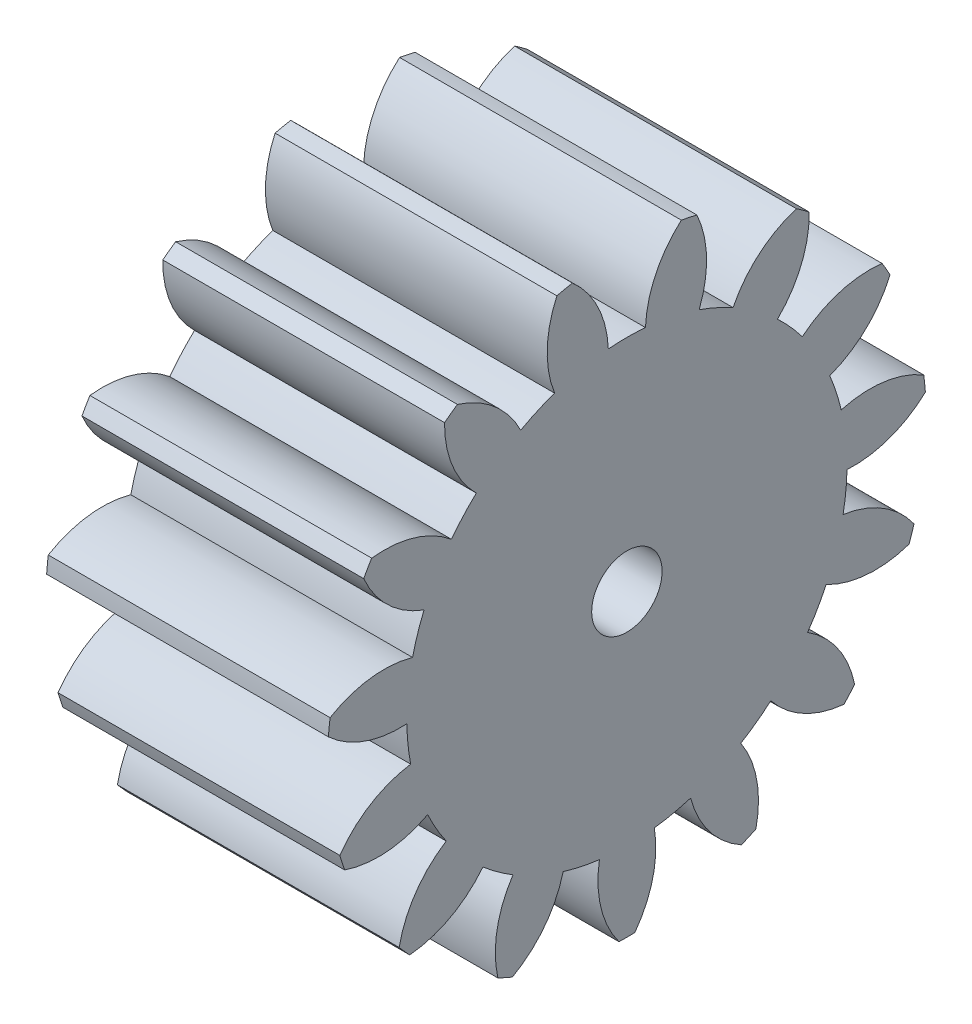
SolidWorks part; units mm, degrees
ref_plane "Plane1" through (0, 0, 0) normal (0, 0, 1) x (1, 0, 0)
ref_plane "Plane2" through (0, 0, 0) normal (0, 1, 0) x (1, 0, 0)
ref_plane "Plane3" through (0, 0, 0) normal (1, 0, 0) x (0, 0, -1)
sketch "HoldingSke" plane through (0, 0, 0) normal (0, 1, 0) x (1, 0, 0)
  line L0 (0, 0) -> (0.3864, -0.1035)
  line L1 (-15, 0) -> (100, 0) construction
  line L2 (0, 0) -> (-2.1039, 2.3779)
  line L3 (0, 0) -> (-11.863, 4.5341)
  line L4 (0, 0) -> (8.3417, 2.2352)
  line L5 (0, 0) -> (-46.8476, -17.4728)
  line L6 (0, 0) -> (-16.5793, -11.1861)
  line L7 (-2.1039, 2.3779) -> (8.6586, 51.2059)
  line L8 (-76.2, 54.61) -> (-75.3, 54.61)
  line L9 (-71.009, 38.7566) -> (-53.1078, 45.2721)
  line L10 (-76.2, 71.12) -> (104.1128, 71.12)
  line L11 (0, 0) -> (-20, 0)
  line L12 (-76.2, 101.6) -> (-76.113, 101.6)
  line L13 (24.9733, 27.94) -> (52.9518, 28.4284)
  line L14 (24.9733, 27.94) -> (24.9743, 27.94)
  line L15 (24.9733, 27.94) -> (100.4006, 29.5858)
  line L16 (-63.627, -2.5) -> (-12.827, -2.5)
  circle A0 centre (0, 0) radius 2.5
  circle A1 centre (0, 0) radius 15.624
  circle A2 centre (0, 0) radius 37.5
  circle A3 centre (0, 0) radius 2.5
  dimension "MHD" = 31.248
  dimension "Hub_dia" = 75
  dimension "Bore" = 5
  dimension "MBD" = 5
  dimension "Num_teeth" = 15
  dimension "Pitch" = 0.4
  dimension "Overall_len" = 50
  dimension "Show_teeth" = 15
  dimension "Thickness" = 20
  dimension "OAL" = 50.0001
  dimension "T_dim" = 0.9
  dimension "Ap" = 20
  dimension "H" = 19.05
  dimension "Pitch_radius" = 180.3128
  dimension "Width" = 20
  dimension "Backlash" = 0.087
  dimension "Addendum_fac" = 1
  dimension "Dedendum_fac" = 1.25
  dimension "Clearance_fac" = 0.25
  dimension "Dedendum_add" = 0.001
  dimension "Module" = 2.5
sketch "BasProSke" plane through (0, 0, 0) normal (0, 1, 0) x (1, 0, 0)
  line L0 (-10, 0) -> (60, 0) construction
  line L1 (0, 0) -> (0, 21.25)
  line L2 (0, 0) -> (20, 0)
  line L3 (20, 0) -> (20, 21.25)
  line L4 (20, 21.25) -> (0, 21.25)
  dimension "Thickness" = 20
  dimension "Diameter" = 42.5
revolve "Base-Revolve" add sketch "BasProSke" angle 360 about L0
sketch "TooCutSke" plane through (0, 0, 0) normal (1, 0, 0) x (0, 0, -1)
  line L1 (0, 0) -> (0, 107) construction
  line L2 (0, 0) -> (-2.112, 18.6307) construction
  line L3 (0, 0) -> (-7.7604, 36.5097) construction
  line L4 (-2.112, 18.6307) -> (-3.8802, 18.2548) construction
  arc A0 (1.3173, 15.5684) -> (-1.3173, 15.5684) centre (0, 0) ccw
  arc A1 (3.8889, 20.917) -> (-3.8889, 20.917) centre (0, 0) ccw
  circle A2 centre (0, 0) radius 18.75 construction
  circle A3 centre (0, 0) radius 17.6192 construction
  arc A4 (-1.3173, 15.5684) -> (-3.8889, 20.917) centre (-8.8109, 15.258) ccw
  arc A5 (3.8889, 20.917) -> (1.3173, 15.5684) centre (8.8109, 15.258) ccw
  dimension "Root_dia" = 31.248
  dimension "Overcut_dia" = 42.5508
  dimension "Pitch_dia" = 37.5
  dimension "Base_dia" = 35.2385
  dimension "Flank_rad" = 7.5
  dimension "Half_ang" = 12
  dimension "Half_CT" = 1.8077
extrude "ToothCut" cut sketch "TooCutSke" along normal through all
fillet "Breaks" [suppressed] radius 0.05
fillet "RootFillets" [suppressed] radius 0.626
pattern_circular "TeethCuts" count 15 every 24 about axis through (-10, 0, 0) along (1, 0, 0) of "ToothCut", "RootFillets", "Breaks"
sketch "HubNeaOneSke" plane through (0, 0, 0) normal (-1, 0, 0) x (0, 0, 1)
  circle A0 centre (0, 0) radius 15.624
  dimension "Diameter" = 31.248
extrude "HubNearOne" [suppressed] add sketch "HubNeaOneSke" along normal blind 30.0001
sketch "HubNeaBotSke" plane through (0, 0, 0) normal (-1, 0, 0) x (0, 0, 1)
  circle A0 centre (0, 0) radius 15.624
  dimension "Diameter" = 31.248
extrude "HubNearBoth" [suppressed] add sketch "HubNeaBotSke" along normal blind 15
ref_plane "FarPln" through (20, 0, 0) normal (1, 0, 0) x (0, 0, -1)
sketch "HubFarSke" plane through (20, 0, 0) normal (1, 0, 0) x (0, 0, -1)
  circle A0 centre (0, 0) radius 15.624
  dimension "Diameter" = 31.248
extrude "HubFar" [suppressed] add sketch "HubFarSke" along normal blind 15
sketch "BorSke" plane through (0, 0, 0) normal (1, 0, 0) x (0, 0, -1)
  circle A0 centre (0, 0) radius 2.5
  dimension "Diameter" = 5
extrude "Bore" cut sketch "BorSke" along normal mid plane 100.0001
sketch "KeySke" plane through (0, 0, 0) normal (1, 0, 0) x (0, 0, -1)
  line L0 (-1, 0) -> (-1, 3.4)
  line L1 (-1, 3.4) -> (1, 3.4)
  line L2 (1, 3.4) -> (1, 0)
  line L3 (0, 0) -> (0, 34) construction
  line L4 (-1, 0) -> (1, 0)
  dimension "Offset" = 3.4
extrude "Keyway" [suppressed] cut sketch "KeySke" along normal mid plane 100.0001
pattern_circular "Keyway2" [suppressed] count 2 every 90 about axis through (-10, 0, 0) along (1, 0, 0)
equation "' \"Module@HoldingSke\" = 6.35"
equation "' \"Num_teeth@HoldingSke\" = 12"
equation "' \"Ap@HoldingSke\" =  20"
equation "' \"Ap@HoldingSke\" = 20"
equation "' \"Width@HoldingSke\" = 0.5 * 25.4"
equation "' \"Hub_dia@HoldingSke\"= 1 * 25.4"
equation "' \"Hub_dia@HoldingSke\" = 1 * 25.4"
equation "' \"Overall_len@HoldingSke\" = 1.0 * 25.4"
equation "' \"Bore@HoldingSke\" = 0.75 * 25.4"
equation "' \"T_dim@HoldingSke\" = 0.1 * 25.4"
equation "' \"Width@KeySke\" = 0.25 * 25.4"
equation "' \"Show_teeth@HoldingSke\" = 13"
equation "' \"Backlash@HoldingSke\" = 0.009 * 25.4"
equation "' \"Addendum_fac@HoldingSke\" = 1.0"
equation "' \"Dedendum_fac@HoldingSke\" = 1.25"
equation "' \"Dedendum_add@HoldingSke\" = 0.00005 * 25.4"
equation "' \"Clearance_fac@HoldingSke\" = 0.25"
equation "\"Pitch@HoldingSke\" = 1 / \"Module@HoldingSke\""
equation "\"Overcut_dia@TooCutSke\" = (\"Num_teeth@HoldingSke\" + 2 * \"Addendum_fac@HoldingSke\") / \"Pitch@HoldingSke\" + 0.002 * 25.4"
equation "\"Pitch_dia@TooCutSke\" = \"Num_teeth@HoldingSke\" / \"Pitch@HoldingSke\""
equation "\"Base_dia@TooCutSke\" = \"Num_teeth@HoldingSke\" / \"Pitch@HoldingSke\" * cos((\"Ap@HoldingSke\"  * 3.14159265 / 180))"
equation "\"Root_dia@TooCutSke\" = (\"Num_teeth@HoldingSke\" + 2) / \"Pitch@HoldingSke\" - 2 * (\"Addendum_fac@HoldingSke\" + \"Dedendum_fac@HoldingSke\") / \"Pitch@HoldingSke\" - \"Dedendum_add@HoldingSke\" * 2"
equation "\"Half_ang@TooCutSke\" = 180 / \"Num_teeth@HoldingSke\""
equation "\"Half_CT@TooCutSke\" = \"Num_teeth@HoldingSke\" / \"Pitch@HoldingSke\" * sin((3.14159265 / 2 / \"Num_teeth@HoldingSke\")) / 2 - 7 * \"Backlash@HoldingSke\" / 4"
equation "\"Flank_rad@TooCutSke\" = \"Num_teeth@HoldingSke\" / \"Pitch@HoldingSke\" / 5"
equation "\"Radius@RootFillets\" = \"Clearance_fac@HoldingSke\" / \"Pitch@HoldingSke\" + \"Dedendum_add@HoldingSke\""
equation "\"Break_rad@Breaks\" = 0.02 / \"Pitch@HoldingSke\""
equation "\"Thickness@HoldingSke\" = \"Width@HoldingSke\""
equation "\"OAL@HoldingSke\" = \"Thickness@HoldingSke\""
equation "\"MHD@HoldingSke\" = (\"Num_teeth@HoldingSke\" + 2) / \"Pitch@HoldingSke\" - 2 * (\"Addendum_fac@HoldingSke\" + \"Dedendum_fac@HoldingSke\")  / \"Pitch@HoldingSke\" - \"Dedendum_add@HoldingSke\" * 2"
equation "\"MBD@HoldingSke\" = (\"Num_teeth@HoldingSke\" + 2) / \"Pitch@HoldingSke\" - 2 * (\"Addendum_fac@HoldingSke\" + \"Dedendum_fac@HoldingSke\")  / \"Pitch@HoldingSke\" - \"Dedendum_add@HoldingSke\" * 2 - 0.002 * 25.4"
equation "\"MHD@HoldingSke\" = ((sgn( \"MHD@HoldingSke\" - \"Hub_dia@HoldingSke\" )-1)*( \"MHD@HoldingSke\" - \"Hub_dia@HoldingSke\" ))/-2+ \"Hub_dia@HoldingSke\""
equation "\"MBD@HoldingSke\" = ((sgn( \"MBD@HoldingSke\" - \"Bore@HoldingSke\" )-1)*( \"MBD@HoldingSke\" - \"Bore@HoldingSke\" ))/-2+ \"Bore@HoldingSke\""
equation "\"OAL@HoldingSke\" = ((sgn( \"OAL@HoldingSke\" - \"Overall_len@HoldingSke\" )+1)*( \"OAL@HoldingSke\" - \"Overall_len@HoldingSke\" ))/2 + \"Overall_len@HoldingSke\" + 0.000002 * 25.4"
equation "\"Num_teeth@TeethCuts\" = int( \"Show_teeth@HoldingSke\" ) + 1"
equation "\"Num_teeth@TeethCuts\" = ((sgn( \"Num_teeth@TeethCuts\" - \"Num_teeth@HoldingSke\" )-1)*( \"Num_teeth@TeethCuts\" - \"Num_teeth@HoldingSke\" ))/-2+ \"Num_teeth@HoldingSke\""
equation "\"Num_teeth@TeethCuts\" = ((sgn( \"Num_teeth@TeethCuts\" - 2.0)+1)*( \"Num_teeth@TeethCuts\" - 2.0))/2 +2.0"
equation "\"Angle@TeethCuts\" = 360.0 / \"Num_teeth@HoldingSke\""
equation "\"Diameter@BasProSke\" = (\"Num_teeth@HoldingSke\" + 2 * \"Addendum_fac@HoldingSke\") / \"Pitch@HoldingSke\""
equation "\"Thickness@BasProSke\"  = \"Thickness@HoldingSke\""
equation "' \"Fillet_rad@BasProSke\" =  \"Thickness@HoldingSke\" * 0.05"
equation "' \"Fillet_rad@BasProSke\" = \"Thickness@HoldingSke\" * 0.05"
equation "\"MHD@HoldingSke\" = ((sgn( \"MHD@HoldingSke\" - \"Root_dia@TooCutSke\" )-1)*( \"MHD@HoldingSke\" - \"Root_dia@TooCutSke\" ))/-2+ \"Root_dia@TooCutSke\""
equation "\"Diameter@HubNeaOneSke\" = \"MHD@HoldingSke\""
equation "\"Length@HubNearOne\" = \"OAL@HoldingSke\" - \"Thickness@BasProSke\""
equation "\"Diameter@HubNeaBotSke\" = \"MHD@HoldingSke\""
equation "\"Length@HubNearBoth\" = ( \"OAL@HoldingSke\" - \"Thickness@BasProSke\" ) / 2.0"
equation "\"Thickness@FarPln\" = \"Thickness@BasProSke\""
equation "\"Diameter@HubFarSke\" = \"MHD@HoldingSke\""
equation "\"Length@HubFar\" = ( \"OAL@HoldingSke\" - \"Thickness@BasProSke\" ) / 2.0"
equation "\"Diameter@BorSke\" = \"MBD@HoldingSke\""
equation "\"D1@Bore\" = \"OAL@HoldingSke\" * 2.0"
equation "\"D1@Keyway\" = \"OAL@HoldingSke\" * 2.0"
equation "\"Offset@KeySke\" = \"T_dim@HoldingSke\" + \"MBD@HoldingSke\" / 2.0"
